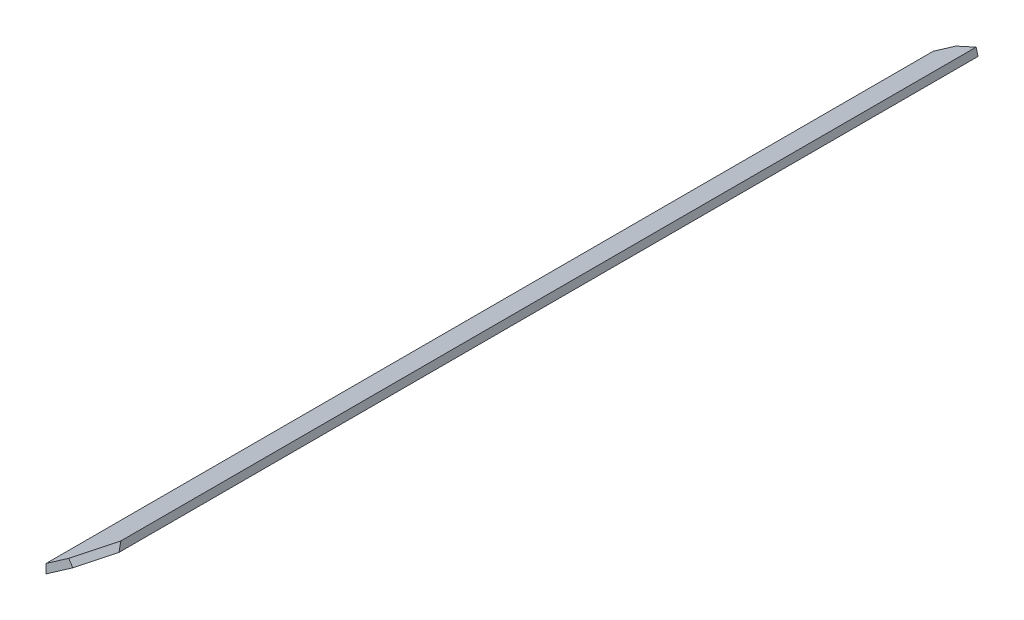
SolidWorks part; units mm, degrees
ref_plane "Alzado" through (0, 0, 0) normal (0, 0, 1) x (1, 0, 0)
ref_plane "Planta" through (0, 0, 0) normal (0, 1, 0) x (1, 0, 0)
ref_plane "Vista lateral" through (0, 0, 0) normal (1, 0, 0) x (0, 0, -1)
sketch "Croquis1" plane through (0, 0, 0) normal (0, 0, 1) x (1, 0, 0)
  line L0 (-2.5, -14.55) -> (-2.5, -98) construction
  line L1 (-2.5, -98) -> (-2.5, -100) construction
  line L2 (4, -95.4746) -> (-2.5, -100)
  line L3 (-2.5, -100) -> (-2.5, -99)
  line L4 (4, -95.4746) -> (4, -94.4746)
  line L5 (4, -94.4746) -> (-2.5, -99)
  dimension "D1" = 4
  dimension "D2" = 2.5
  dimension "D3" = 94.4746
  dimension "D4" = 95.4746
  dimension "D5" = 99
extrude "Saliente-Extruir2" add sketch "Croquis1" along normal up to vertex (21 mm away) and the other way up to vertex (77 mm away)
sketch "Croquis3" plane through (45.607, -65.5073, 0) normal (-0.5714, 0.8207, 0) x (0.8207, 0.5714, 0)
  line L2 (-50.6976, -21) -> (-50.6976, 77) construction
  line L11 (-50.6976, 77) -> (-50.6976, 75.2314)
  line L12 (-22.2871, 64.9089) -> (-51.269, 75.439) construction
  line L13 (-50.6976, 75.2314) -> (-55.5716, 77)
  line L14 (-55.5716, 77) -> (-50.6976, 75.439) construction
  line L15 (-55.5716, 77) -> (-50.6976, 77)
  line L16 (-50.6976, -21) -> (-50.6976, -19.2314)
  line L17 (-51.269, -19.439) -> (-22.2871, -8.9089) construction
  line L18 (-50.6976, -19.2314) -> (-55.5716, -21)
  line L19 (-50.6976, -21) -> (-58.6178, -21) construction
  line L20 (-55.5716, -21) -> (-50.6976, -21)
extrude "Cortar-Extruir2" cut sketch "Croquis3" against normal up to vertex
